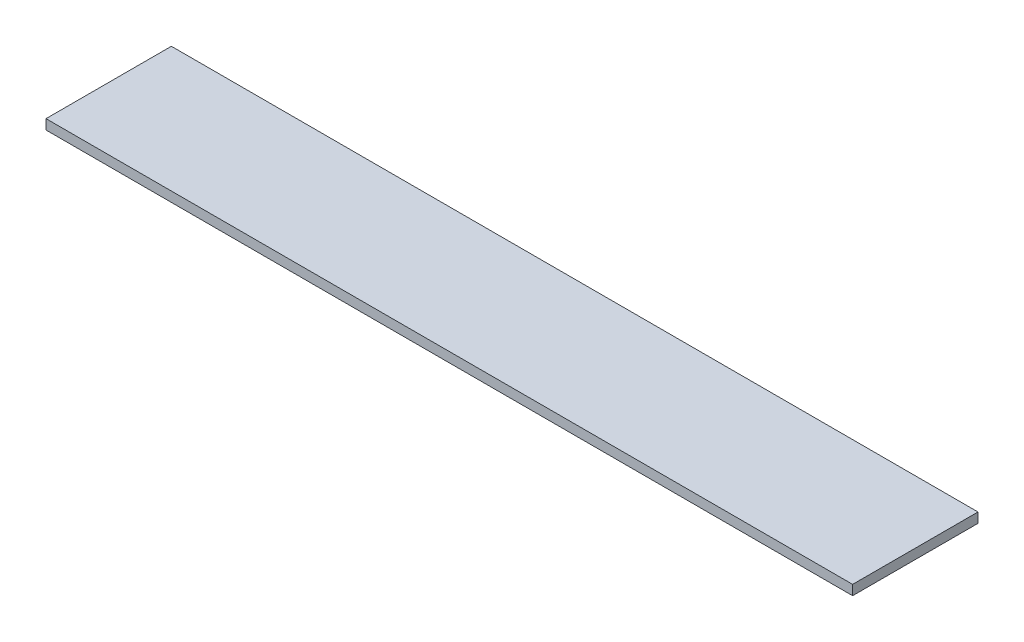
SolidWorks part; units mm, degrees
material "6063-T1"
ref_plane "Front Plane" through (0, 0, 0) normal (0, 0, 1) x (1, 0, 0)
ref_plane "Top Plane" through (0, 0, 0) normal (0, 1, 0) x (1, 0, 0)
ref_plane "Right Plane" through (0, 0, 0) normal (1, 0, 0) x (0, 0, -1)
sketch "Sketch1" plane through (0, 0, 0) normal (0, 1, 0) x (1, 0, 0)
  line L1 (-81.715, -12.7) -> (81.715, -12.7)
  line L2 (-81.715, -12.7) -> (-81.715, 12.7)
  line L3 (-81.715, 12.7) -> (81.715, 12.7)
  line L4 (81.715, -12.7) -> (81.715, 12.7)
  line L5 (-81.715, -12.7) -> (81.715, 12.7) construction
  line L6 (-81.715, 12.7) -> (81.715, -12.7) construction
  point P0 (0, 0)
  dimension "D1" = 25.4
  dimension "D2" = 163.43
extrude "Boss-Extrude1" add sketch "Sketch1" along normal blind 2
